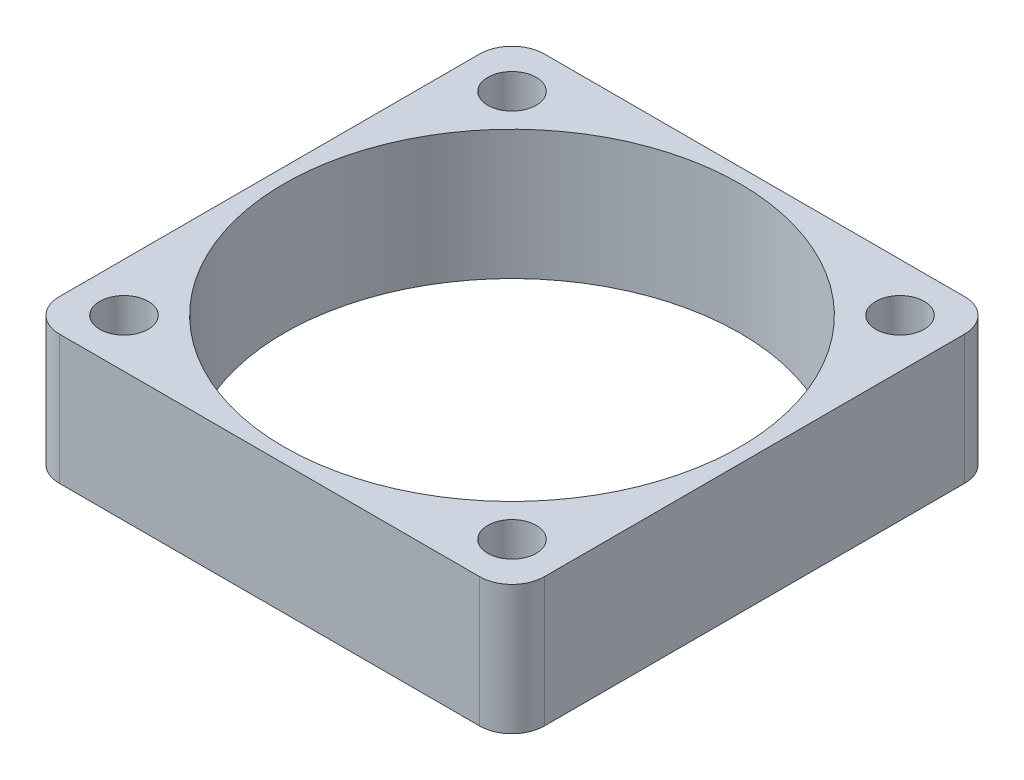
SolidWorks part; units mm, degrees
ref_plane "Front Plane" through (0, 0, 0) normal (0, 0, 1) x (1, 0, 0)
ref_plane "Top Plane" through (0, 0, 0) normal (0, 1, 0) x (1, 0, 0)
ref_plane "Right Plane" through (0, 0, 0) normal (1, 0, 0) x (0, 0, -1)
sketch "Sketch1" plane through (0, 0, 0) normal (0, 1, 0) x (1, 0, 0)
  line L1 (15, 15) -> (-15, 15)
  line L2 (15, 15) -> (15, -15)
  line L3 (15, -15) -> (-15, -15)
  line L4 (-15, 15) -> (-15, -15)
  line L5 (15, 15) -> (-15, -15) construction
  line L6 (15, -15) -> (-15, 15) construction
  point P0 (0, 0)
  dimension "D1" = 30
  dimension "D2" = 30
extrude "Boss-Extrude1" add sketch "Sketch1" along normal blind 8
fillet "Fillet1" radius 2 4 edges at (-15, 4, -15) (-15, 4, 15) (15, 4, -15) (15, 4, 15)
sketch "Sketch2" plane through (0, 8, 0) normal (0, 1, 0) x (1, 0, 0)
  line L0 (-14.4142, 14.4142) -> (14.4142, -14.4142) construction
  line L1 (-14.4142, -14.4142) -> (14.4142, 14.4142) construction
  circle A0 centre (0, 0) radius 16.9706 construction
  arc A1 (-13, 15) -> (-15, 13) centre (-13, 13) ccw construction
  arc A2 (13, -15) -> (15, -13) centre (13, -13) ccw construction
  arc A3 (-15, -13) -> (-13, -15) centre (-13, -13) ccw construction
  arc A4 (15, 13) -> (13, 15) centre (13, 13) ccw construction
  circle A5 centre (-12, 12) radius 1.5
  circle A6 centre (12, 12) radius 1.5
  circle A7 centre (-12, -12) radius 1.5
  circle A8 centre (12, -12) radius 1.5
  dimension "D1" = 24
  dimension "D2" = 3
extrude "Cut-Extrude1" cut sketch "Sketch2" against normal blind 8
sketch "Sketch3" plane through (0, 8, 0) normal (0, 1, 0) x (1, 0, 0)
  line L0 (-15, 13) -> (-15, -13) construction
  circle A0 centre (0, 0) radius 14.1
  dimension "D1" = 0.9
extrude "Cut-Extrude2" cut sketch "Sketch3" against normal blind 8
